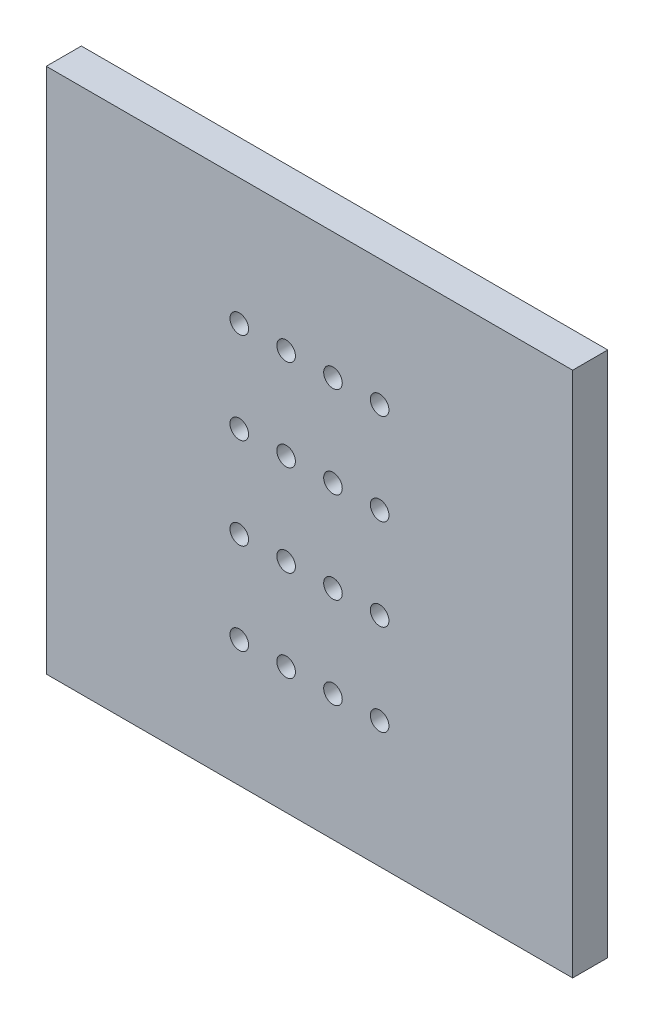
SolidWorks part; units mm, degrees
ref_plane "Plan de face" through (0, 0, 0) normal (0, 0, 1) x (1, 0, 0)
ref_plane "Plan de dessus" through (0, 0, 0) normal (0, 1, 0) x (1, 0, 0)
ref_plane "Plan de droite" through (0, 0, 0) normal (1, 0, 0) x (0, 0, -1)
sketch "Esquisse1" plane through (0, 0, 0) normal (0, 0, 1) x (1, 0, 0)
  line L1 (-15, -15) -> (15, -15)
  line L2 (-15, -15) -> (-15, 15)
  line L3 (-15, 15) -> (15, 15)
  line L4 (15, -15) -> (15, 15)
  line L5 (-15, -15) -> (15, 15) construction
  line L6 (-15, 15) -> (15, -15) construction
  point P0 (0, 0)
extrude "Base_Plate" add sketch "Esquisse1" along normal blind 2
sketch "Sketch_Perforations" plane through (0, 0, 2) normal (0, 0, 1) x (1, 0, 0)
  circle A0 centre (-4, -7.8) radius 0.53
  circle A1 centre (-4, -2.6) radius 0.53
  circle A2 centre (-4, 2.6) radius 0.53
  circle A3 centre (-4, 7.8) radius 0.53
  circle A4 centre (-1.33, -7.8) radius 0.53
  circle A5 centre (-1.33, -2.6) radius 0.53
  circle A6 centre (-1.33, 2.6) radius 0.53
  circle A7 centre (-1.33, 7.8) radius 0.53
  circle A8 centre (1.34, -7.8) radius 0.53
  circle A9 centre (1.34, -2.6) radius 0.53
  circle A10 centre (1.34, 2.6) radius 0.53
  circle A11 centre (1.34, 7.8) radius 0.53
  circle A12 centre (4, -7.8) radius 0.53
  circle A13 centre (4, -2.6) radius 0.53
  circle A14 centre (4, 2.6) radius 0.53
  circle A15 centre (4, 7.8) radius 0.53
extrude "Cut_Perforations" cut sketch "Sketch_Perforations" against normal blind 10
